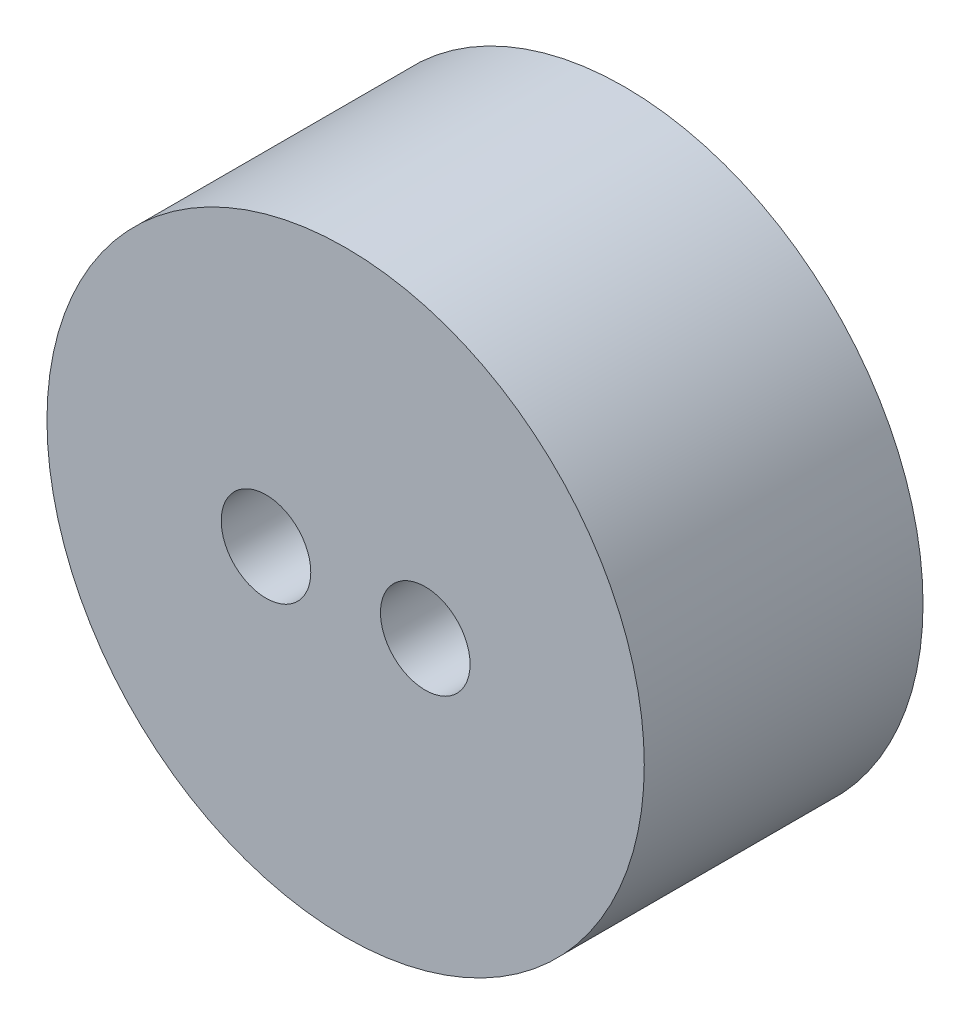
SolidWorks part; units mm, degrees
material "ｼﾘｺﾝ ｺﾞﾑ"
ref_plane "正面" through (0, 0, 0) normal (0, 0, 1) x (1, 0, 0)
ref_plane "平面" through (0, 0, 0) normal (0, 1, 0) x (1, 0, 0)
ref_plane "右側面" through (0, 0, 0) normal (1, 0, 0) x (0, 0, -1)
sketch "ｽｹｯﾁ1" plane through (0, 0, 0) normal (0, 0, 1) x (1, 0, 0)
  circle A0 centre (0, 0) radius 15
  dimension "D1" = 30
extrude "ﾎﾞｽ - 押し出し1" add sketch "ｽｹｯﾁ1" along normal blind 14
sketch "ｽｹｯﾁ2" plane through (0, 0, 14) normal (0, 0, 1) x (1, 0, 0)
  line L0 (4, 0) -> (-4, 0) construction
  point P5 (0, 0)
  dimension "D1" = 8
hole_wizard "M4 すきま穴1" positions "ｽｹｯﾁ3" profile "ｽｹｯﾁ4" hole size "M4" standard "JIS" end condition through all
sketch "ｽｹｯﾁ3" plane through (0, 0, 14) normal (0, 0, 1) x (1, 0, 0)
  point P0 (-4, 0)
  point P3 (4, 0)
sketch "ｽｹｯﾁ4" plane through (-4, 0, 14) normal (1, 0, 0) x (0, -1, 0)
  line L0 (0, 0) -> (0, 14)
  line L1 (0, 14) -> (2.25, 14)
  line L2 (2.25, 14) -> (2.25, 0)
  line L5 (2.25, 0) -> (0, 0)
  line L11 (0, -6.35) -> (0, 107.95) construction
  dimension "通し穴の直径" = 4.5
  dimension "通し穴の深さ" = 14
